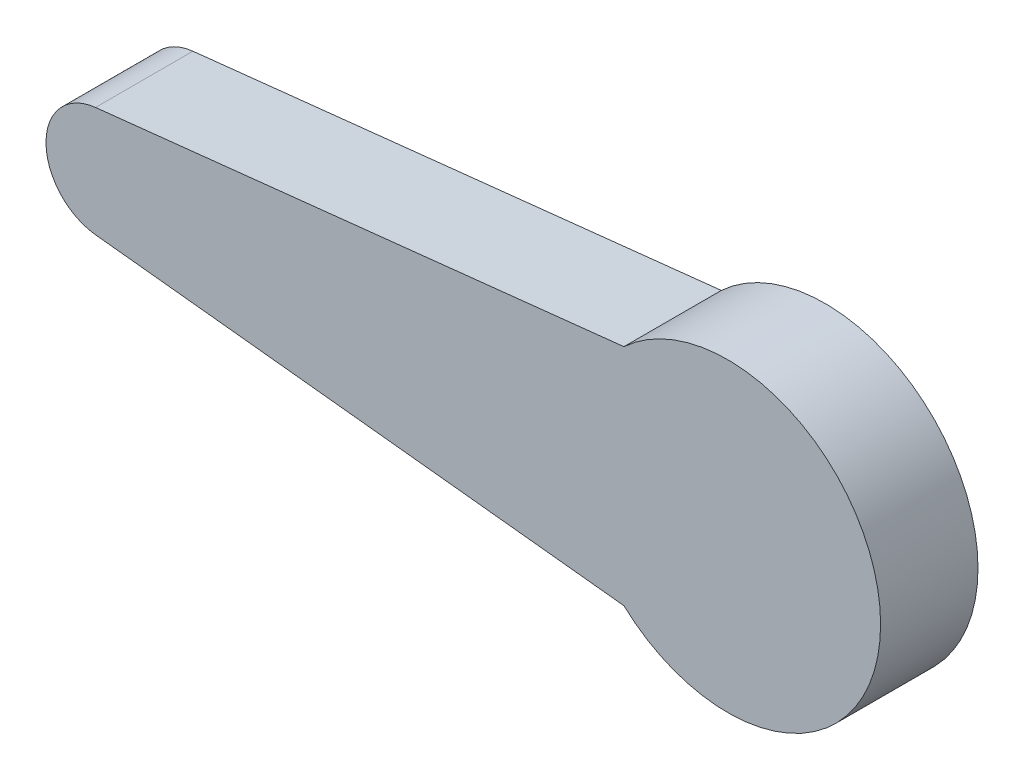
SolidWorks part; units mm, degrees
ref_plane "Front Plane" through (0, 0, 0) normal (0, 0, 1) x (1, 0, 0)
ref_plane "Top Plane" through (0, 0, 0) normal (0, 1, 0) x (1, 0, 0)
ref_plane "Right Plane" through (0, 0, 0) normal (1, 0, 0) x (0, 0, -1)
sketch "Sketch1" plane through (0, 0, 0) normal (0, 0, 1) x (1, 0, 0)
  line L0 (-2.3083, 2.4981) -> (9.375, 3.1901)
  line L1 (9.375, -3.1901) -> (-2.3083, -2.4981)
  spline S0 degree 3 poles (9.375, 3.1901) (9.7438, 3.5351) (10.5421, 3.8854) (11.7399, 4.0538) (12.7816, 3.904) (13.6476, 3.5884) (14.1725, 3.1236) (14.7494, 2.728) (15.2394, 2.0155) (15.6535, 1.0509) (15.789, -0.0007) (15.6517, -1.0481) (15.2469, -2.0252) (14.6033, -2.864) (13.7643, -3.5078) (12.7878, -3.9119) (11.7382, -4.0517) (10.5429, -3.8863) (9.7436, -3.5348) (9.375, -3.1901) knots 0 0 0 0 0.085137 0.144403 0.203669 0.262935 0.297503 0.322201 0.381468 0.440734 0.5 0.559266 0.618532 0.677799 0.737065 0.796331 0.855597 0.914863 1 1 1 1
  spline S1 degree 3 poles (-2.3083, -2.4981) (-2.7303, -2.4987) (-3.3653, -2.3178) (-4.0519, -1.7912) (-4.4545, -1.2665) (-4.7076, -0.6556) (-4.7939, 0) (-4.7076, 0.6556) (-4.4545, 1.2665) (-4.0519, 1.7912) (-3.3653, 2.3178) (-2.7303, 2.4987) (-2.3083, 2.4981) knots 0 0 0 0 0.162547 0.246911 0.331273 0.415637 0.5 0.584363 0.668727 0.753089 0.837453 1 1 1 1
sketch "Sketch2" plane through (0, 0, 0) normal (0, 0, 1) x (1, 0, 0)
  line L1 (7.9369, 4.6075) -> (-13.7648, 2.2651)
  line L4 (-13.7648, -2.2651) -> (7.9369, -4.6075)
  arc A3 (-13.7648, 2.2651) -> (-13.7648, -2.2651) centre (-13.5203, 0) ccw
  arc A4 (7.9369, 4.6075) -> (7.9369, -4.6075) centre (12.2014, 0) cw
  point P1 (-15.7986, 0)
  dimension "D1" = 28
  dimension "D3" = 6.2781
extrude "Boss-Extrude6" add sketch "Sketch2" along normal blind 4 contours A4 L4 A3 L1
extrude "Cut-Extrude1" cut sketch "Sketch1" along normal blind 2
